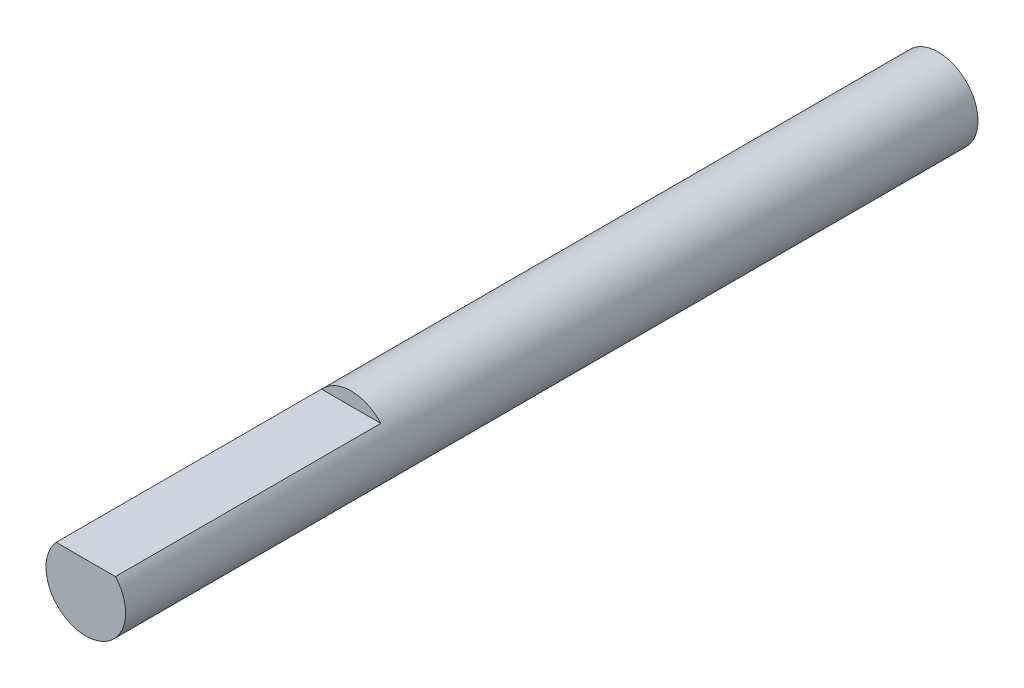
SolidWorks part; units mm, degrees
ref_plane "Front Plane" through (0, 0, 0) normal (0, 0, 1) x (1, 0, 0)
ref_plane "Top Plane" through (0, 0, 0) normal (0, 1, 0) x (1, 0, 0)
ref_plane "Right Plane" through (0, 0, 0) normal (1, 0, 0) x (0, 0, -1)
sketch "Sketch1" plane through (0, 0, 0) normal (0, 0, 1) x (1, 0, 0)
  circle A0 centre (0, 0) radius 1.5
  dimension "D1" = 3
extrude "Boss-Extrude1" add sketch "Sketch1" along normal mid plane 32.125
sketch "Sketch2" plane through (0, 0, 16.0625) normal (0, 0, 1) x (1, 0, 0)
  line L0 (1.118, 1) -> (-1.118, 1)
  circle A0 centre (0, 0) radius 1.5 construction
  arc A1 (-1.118, 1) -> (1.118, 1) centre (0, 0) cw
  dimension "D1" = 1
extrude "Cut-Extrude1" cut sketch "Sketch2" against normal blind 10
